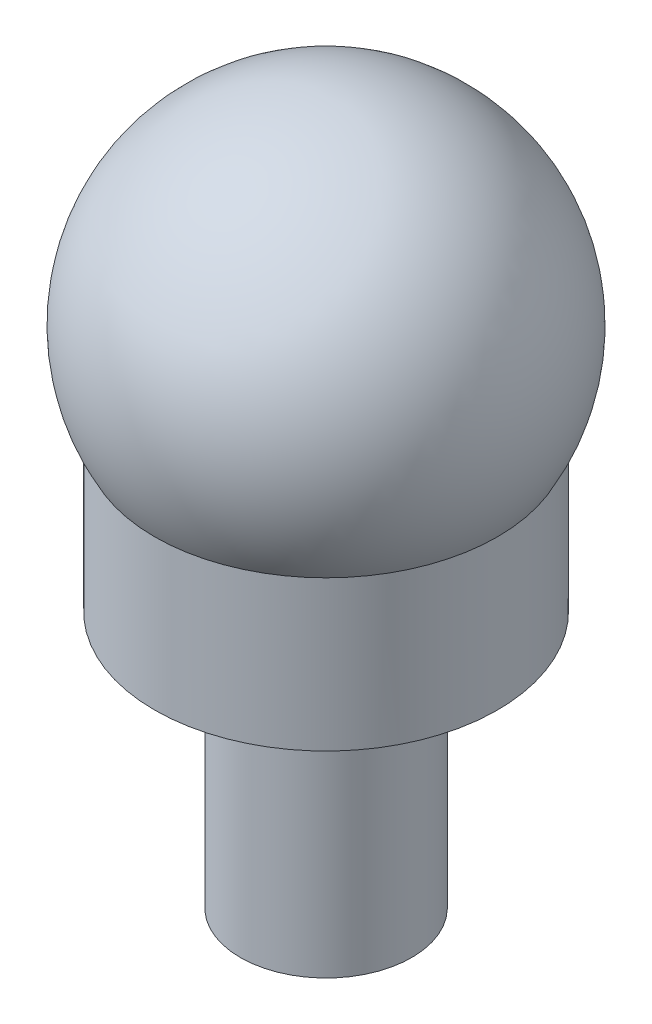
SolidWorks part; units mm, degrees
ref_plane "Front Plane" through (0, 0, 0) normal (0, 0, 1) x (1, 0, 0)
ref_plane "Top Plane" through (0, 0, 0) normal (0, 1, 0) x (1, 0, 0)
ref_plane "Right Plane" through (0, 0, 0) normal (1, 0, 0) x (0, 0, -1)
sketch "Sketch1" plane through (0, 0, 0) normal (0, 1, 0) x (1, 0, 0)
  circle A0 centre (0, 0) radius 4
extrude "Boss-Extrude1" add sketch "Sketch1" along normal blind 12
sketch "Sketch3" plane through (0, 12, 0) normal (0, 1, 0) x (1, 0, 0)
  circle A0 centre (0, 0) radius 8
extrude "Boss-Extrude2" add sketch "Sketch3" along normal blind 7
sketch "Sketch4" plane through (0, 0, 0) normal (0, 0, 1) x (1, 0, 0)
  line L0 (8, 19) -> (-8, 19) construction
  line L1 (0, 28.1194) -> (0, 19)
  line L2 (0, 19) -> (8, 19)
  line L3 (0, 28.1194) -> (0, 32.7679)
  arc A0 (8, 19) -> (0, 32.7679) centre (0, 23.5597) ccw
revolve "Revolve2" add sketch "Sketch4" angle 360 about L1
